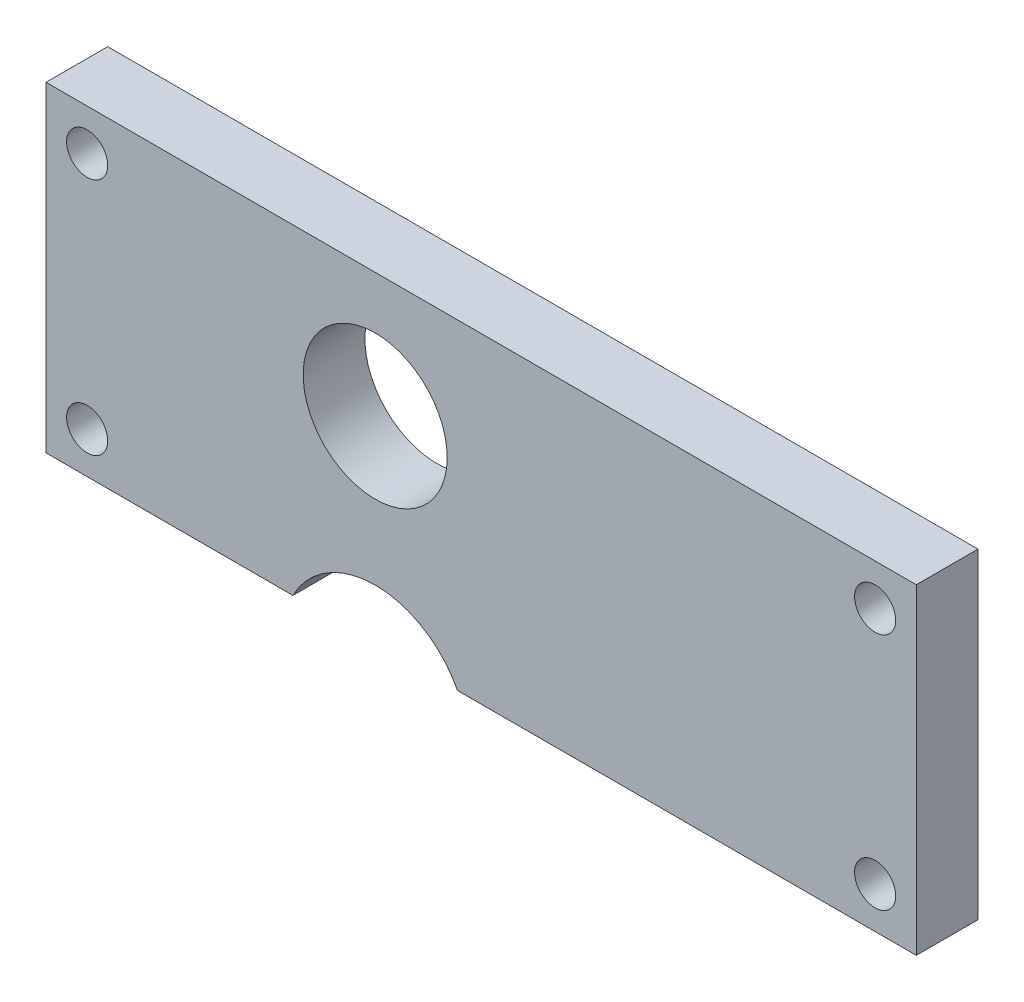
SolidWorks part; units mm, degrees
material "1060 Alloy"
ref_plane "Front Plane" through (0, 0, 0) normal (0, 0, 1) x (1, 0, 0)
ref_plane "Top Plane" through (0, 0, 0) normal (0, 1, 0) x (1, 0, 0)
ref_plane "Right Plane" through (0, 0, 0) normal (1, 0, 0) x (0, 0, -1)
sketch "Sketch1" plane through (0, 0, 0) normal (0, 0, 1) x (1, 0, 0)
  line L1 (0, 0) -> (42.3, 0)
  line L2 (0, 0) -> (0, 15.6)
  line L3 (0, 15.6) -> (42.3, 15.6)
  line L4 (42.3, 0) -> (42.3, 15.6)
  dimension "D1" = 42.3
  dimension "D2" = 15.6
extrude "Boss-Extrude1" add sketch "Sketch1" along normal blind 3
sketch "Sketch2" plane through (0, 0, 3) normal (0, 0, 1) x (1, 0, 0)
  line L0 (0, 0) -> (42.3, 0) construction
  line L1 (2, 2) -> (40.3, 2) construction
  line L2 (2, 2) -> (2, 13.6) construction
  line L3 (2, 13.6) -> (40.3, 13.6) construction
  line L4 (40.3, 2) -> (40.3, 13.6) construction
  line L5 (2, 7.8) -> (0, 7.8) construction
  line L6 (0, 15.6) -> (0, 0) construction
  circle A0 centre (2, 13.6) radius 1
  circle A1 centre (40.3, 13.6) radius 1
  circle A2 centre (40.3, 2) radius 1
  circle A3 centre (2, 2) radius 1
  point P6 (21.15, 0)
  point P7 (21.15, 2)
  dimension "D3" = 2
  dimension "D1" = 38.3
  dimension "D2" = 11.6
extrude "Cut-Extrude1" cut sketch "Sketch2" against normal through all
sketch "Sketch3" plane through (0, 0, 3) normal (0, 0, 1) x (1, 0, 0)
  line L0 (0, 15.6) -> (0, 0) construction
  line L1 (42.3, 15.6) -> (0, 15.6) construction
  circle A0 centre (16, 9.55) radius 3.5
  dimension "D1" = 7
  dimension "D2" = 16
  dimension "D3" = 6.05
extrude "Cut-Extrude2" cut sketch "Sketch3" against normal through all
sketch "Sketch4" plane through (0, 0, 3) normal (0, 0, 1) x (1, 0, 0)
  line L0 (0, 0) -> (42.3, 0) construction
  line L1 (12, 0) -> (20, 0)
  arc A0 (12, 0) -> (20, 0) centre (16, -2.0616) cw
  circle A1 centre (16, 9.55) radius 3.5 construction
  circle A2 centre (16, 9.55) radius 3.5 construction
  dimension "D1" = 4.5
  dimension "D2" = 8
extrude "Cut-Extrude3" cut sketch "Sketch4" against normal through all
